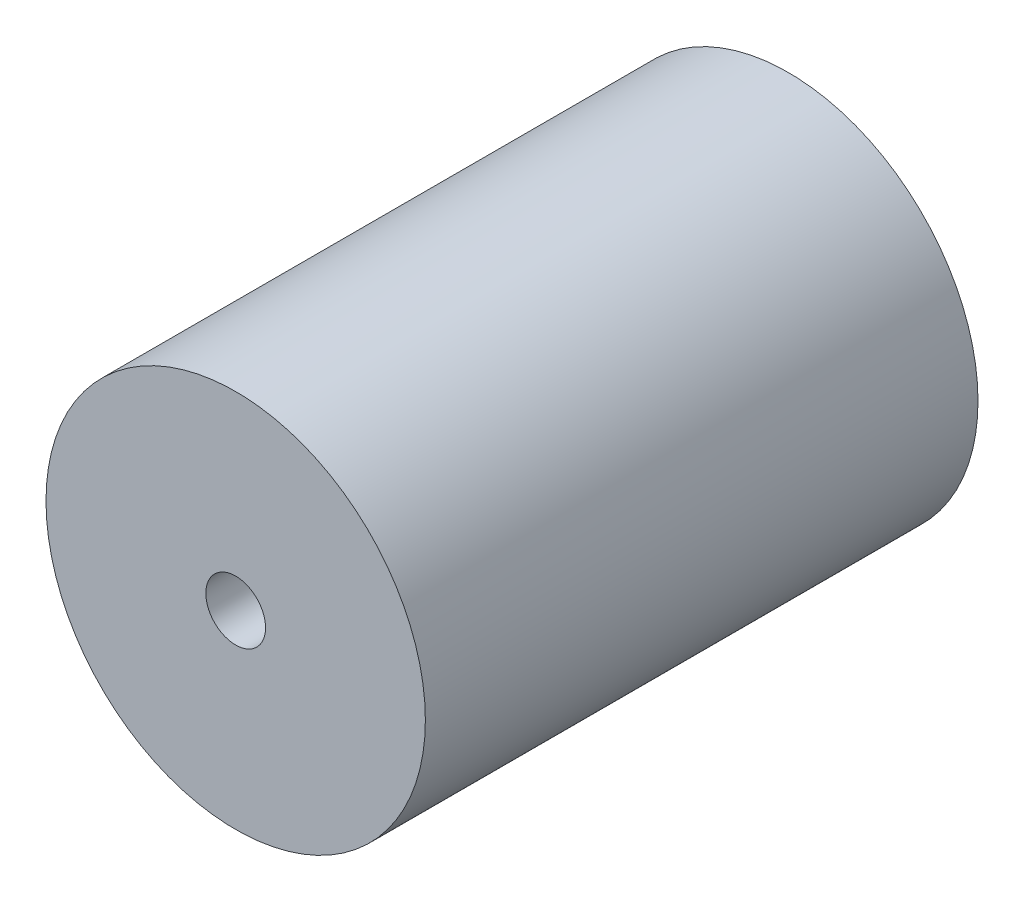
SolidWorks part; units mm, degrees
ref_plane "Front Plane" through (0, 0, 0) normal (0, 0, 1) x (1, 0, 0)
ref_plane "Top Plane" through (0, 0, 0) normal (0, 1, 0) x (1, 0, 0)
ref_plane "Right Plane" through (0, 0, 0) normal (1, 0, 0) x (0, 0, -1)
sketch "Sketch1" plane through (0, 0, 0) normal (0, 0, 1) x (1, 0, 0)
  line L1 (-36.5147, 0) -> (52.8833, 0) construction
  line L2 (0, 9.5) -> (0, -9.5) construction
  circle A0 centre (0, 0) radius 25.4
  circle A1 centre (0, 0) radius 4
  point P3 (0, 0)
  point P19 (0, 0)
  dimension "D1" = 50.8
  dimension "D2" = 19
  dimension "D3" = 8
extrude "Boss-Extrude1" add sketch "Sketch1" along normal mid plane 74
